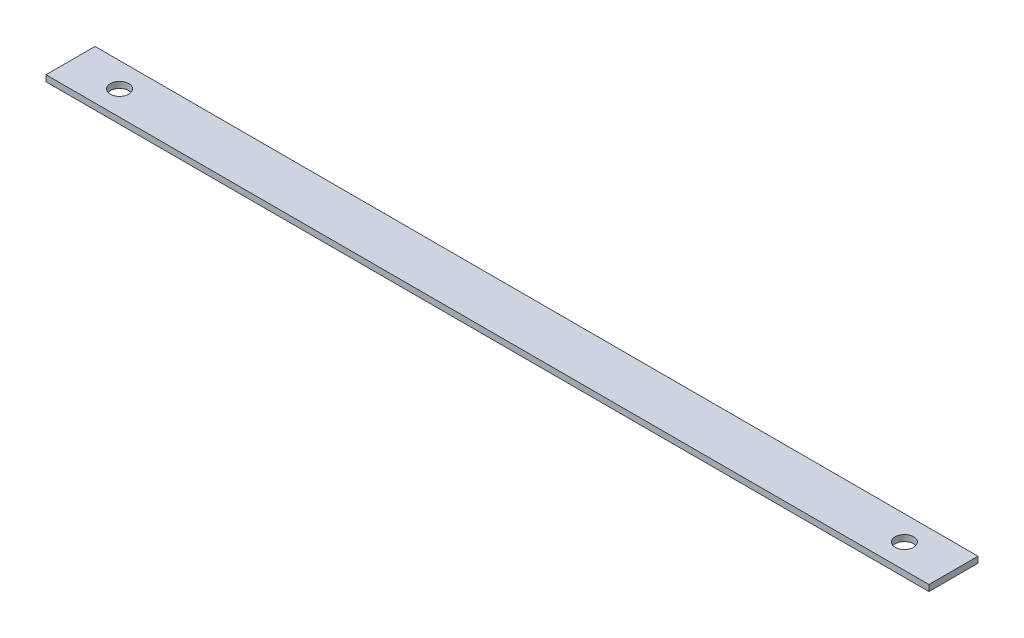
SolidWorks part; units mm, degrees
ref_plane "Front Plane" through (0, 0, 0) normal (0, 0, 1) x (1, 0, 0)
ref_plane "Top Plane" through (0, 0, 0) normal (0, 1, 0) x (1, 0, 0)
ref_plane "Right Plane" through (0, 0, 0) normal (1, 0, 0) x (0, 0, -1)
sketch "Sketch1" plane through (0, 0, 0) normal (0, 1, 0) x (1, 0, 0)
  line L1 (228.6, -12.7) -> (-228.6, -12.7)
  line L2 (228.6, -12.7) -> (228.6, 12.7)
  line L3 (228.6, 12.7) -> (-228.6, 12.7)
  line L4 (-228.6, -12.7) -> (-228.6, 12.7)
  line L5 (228.6, -12.7) -> (-228.6, 12.7) construction
  line L6 (228.6, 12.7) -> (-228.6, -12.7) construction
  point P0 (0, 0)
  dimension "D1" = 25.4
  dimension "D2" = 457.2
extrude "Boss-Extrude1" add sketch "Sketch1" along normal blind 3.175
sketch "Sketch2" plane through (0, 3.175, 0) normal (0, 1, 0) x (1, 0, 0)
  line L0 (203.2, 0) -> (-203.2, 0) construction
  line L1 (0, 0) -> (0, -34.3876) construction
  circle A0 centre (-203.2, 0) radius 4.7625
  circle A1 centre (203.2, 0) radius 4.7625
  point P4 (0, 0)
  dimension "D1" = 9.525
  dimension "D2" = 406.4
extrude "Cut-Extrude1" cut sketch "Sketch2" against normal through all
